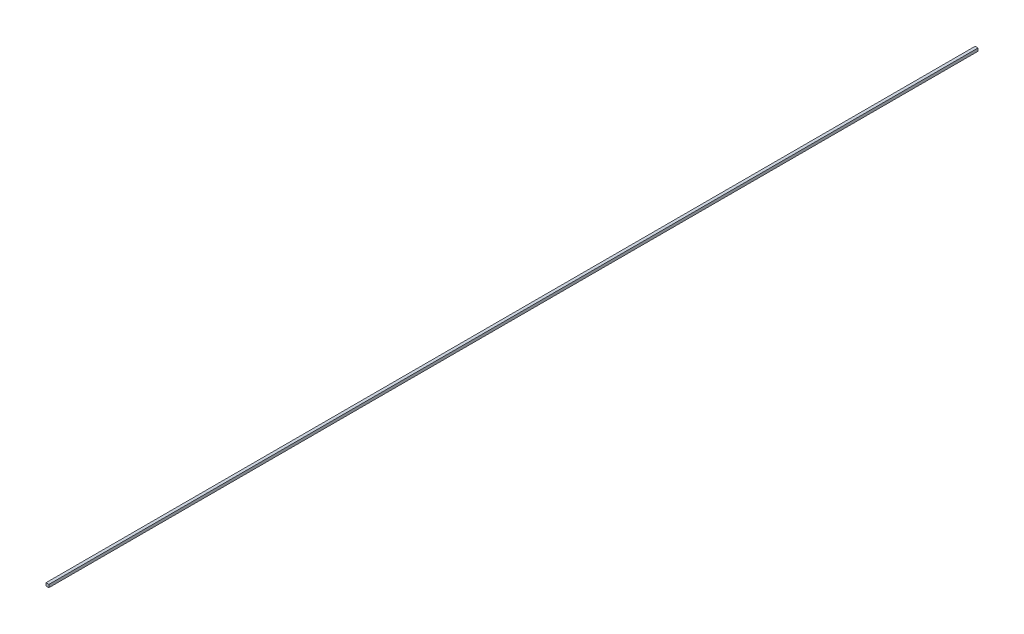
SolidWorks part; units mm, degrees
material "ﾊﾞﾙｻ"
ref_plane "正面" through (0, 0, 0) normal (0, 0, 1) x (1, 0, 0)
ref_plane "平面" through (0, 0, 0) normal (0, 1, 0) x (1, 0, 0)
ref_plane "右側面" through (0, 0, 0) normal (1, 0, 0) x (0, 0, -1)
sketch "ｽｹｯﾁ1" plane through (0, 0, 0) normal (0, 0, 1) x (1, 0, 0)
  line L1 (-1, 1) -> (1, 1)
  line L2 (-1, 1) -> (-1, -1)
  line L3 (-1, -1) -> (1, -1)
  line L4 (1, 1) -> (1, -1)
  line L5 (-1, 1) -> (1, -1) construction
  line L6 (-1, -1) -> (1, 1) construction
  point P0 (0, 0)
  dimension "D1" = 2
extrude "ﾎﾞｽ - 押し出し1" add sketch "ｽｹｯﾁ1" along normal blind 640.8
